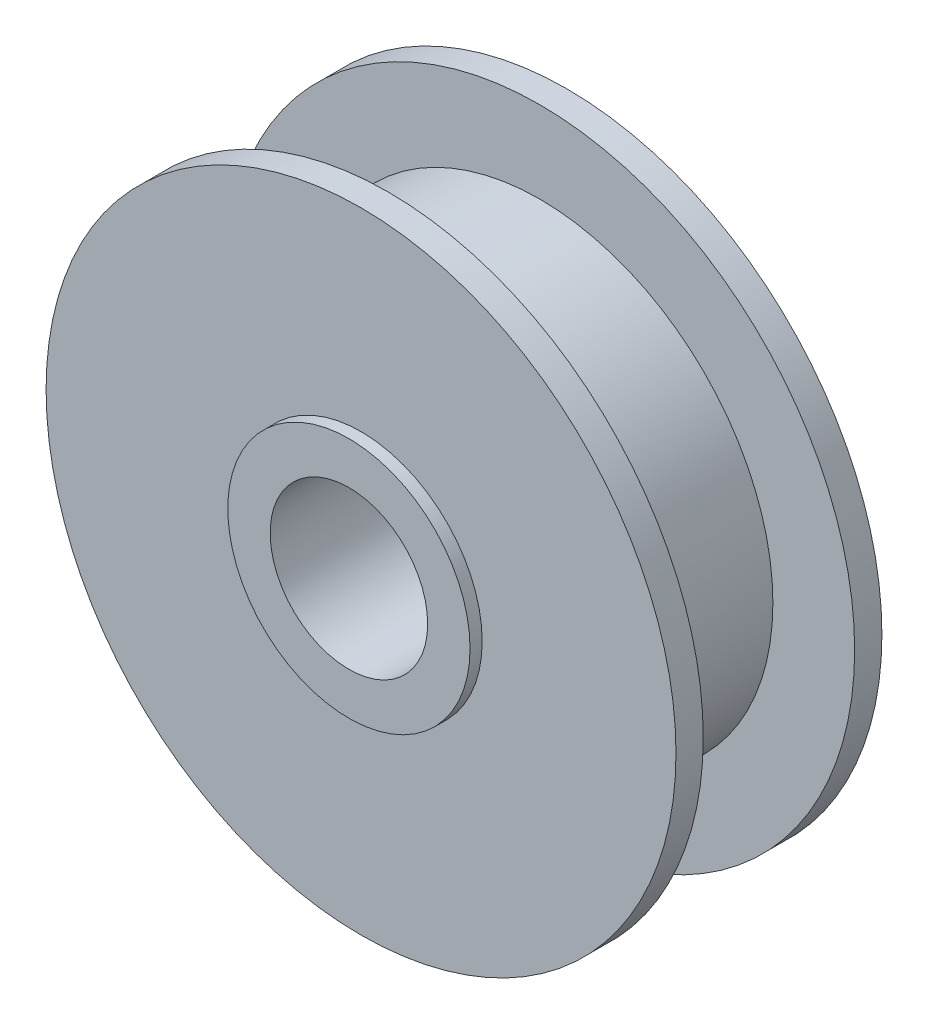
SolidWorks part; units mm, degrees
ref_plane "Front Plane" through (0, 0, 0) normal (0, 0, 1) x (1, 0, 0)
ref_plane "Top Plane" through (0, 0, 0) normal (0, 1, 0) x (1, 0, 0)
ref_plane "Right Plane" through (0, 0, 0) normal (1, 0, 0) x (0, 0, -1)
sketch "Sketch1" plane through (0, 0, 0) normal (1, 0, 0) x (0, 0, -1)
  line L0 (-1.9, 1.3) -> (-1.9, 2)
  line L1 (-1.9, 2) -> (-1.7, 2)
  line L2 (-1.7, 2) -> (-1.7, 5.2)
  line L3 (-1.7, 5.2) -> (-1.25, 5.2)
  line L4 (-1.25, 5.2) -> (-1.25, 3.85)
  line L5 (-1.25, 3.85) -> (1.25, 3.85)
  line L6 (1.25, 3.85) -> (1.25, 5.2)
  line L7 (1.25, 5.2) -> (1.7, 5.2)
  line L8 (1.7, 5.2) -> (1.7, 2)
  line L9 (1.7, 2) -> (1.9, 2)
  line L10 (1.9, 2) -> (1.9, 1.3)
  line L11 (1.9, 1.3) -> (-1.9, 1.3)
  line L12 (-1.9, 0) -> (1.9, 0) construction
  dimension "D1" = 5.2
  dimension "D2" = 2
  dimension "D3" = 2.5
  dimension "D4" = 1.3
  dimension "D5" = 3.85
  dimension "D6" = 0.45
  dimension "D7" = 0.2
  dimension "D8" = 1.9
revolve "Revolve1" add sketch "Sketch1" angle 360 about L12
